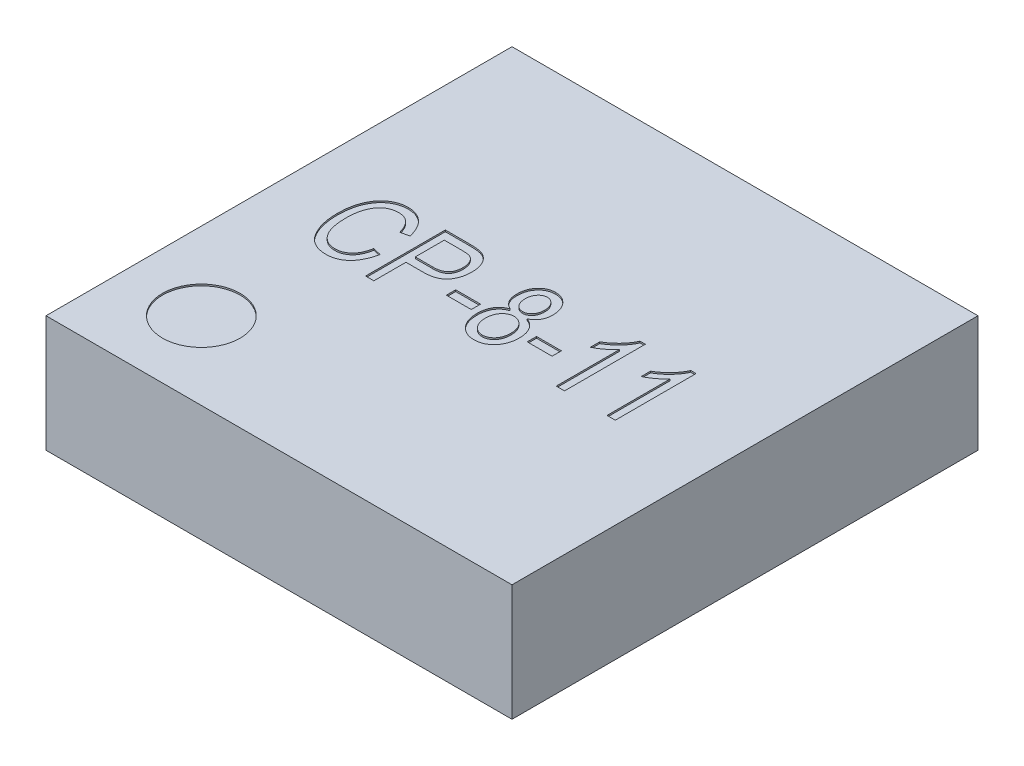
SolidWorks part; units mm, degrees
ref_plane "Front Plane" through (0, 0, 0) normal (0, 0, 1) x (1, 0, 0)
ref_plane "Top Plane" through (0, 0, 0) normal (0, 1, 0) x (1, 0, 0)
ref_plane "Right Plane" through (0, 0, 0) normal (1, 0, 0) x (0, 0, -1)
sketch "Sketch1" plane through (0, 0, 0) normal (0, 1, 0) x (1, 0, 0)
  line L1 (-1.5, -1.5) -> (1.5, -1.5)
  line L2 (-1.5, -1.5) -> (-1.5, 1.5)
  line L3 (-1.5, 1.5) -> (1.5, 1.5)
  line L4 (1.5, -1.5) -> (1.5, 1.5)
  line L5 (-1.5, -1.5) -> (1.5, 1.5) construction
  line L6 (-1.5, 1.5) -> (1.5, -1.5) construction
  point P0 (0, 0)
  dimension "D1" = 3
extrude "Boss-Extrude1" add sketch "Sketch1" along normal blind 0.75
sketch "Sketch2" plane through (0, 0.75, 0) normal (0, 1, 0) x (1, 0, 0)
  line L0 (-1.5, -1.5) -> (1.5, -1.5) construction
  line L1 (-1.5, 1.5) -> (-1.5, -1.5) construction
  circle A0 centre (-1, -1) radius 0.25
  dimension "D3" = 0.5
  dimension "D1" = 0.5
  dimension "D2" = 0.5
extrude "Cut-Extrude1" cut sketch "Sketch2" against normal blind 0.01
sketch "Sketch5" plane through (0, 0.75, 0) normal (0, 1, 0) x (1, 0, 0)
  line L0 (-1.5, -0.25) -> (1.5, -0.25) construction
  line L1 (-1.5, 1.5) -> (-1.5, -1.5) construction
  line L2 (1.5, -1.5) -> (1.5, 1.5) construction
  line L3 (-0.4125, 0) -> (0.4125, 0) construction
  text T0 "  CP-8-11" font "Arial Narrow" height in points 2
  dimension "D1" = 0.25
extrude "Cut-Extrude3" cut sketch "Sketch5" against normal blind 0.01
